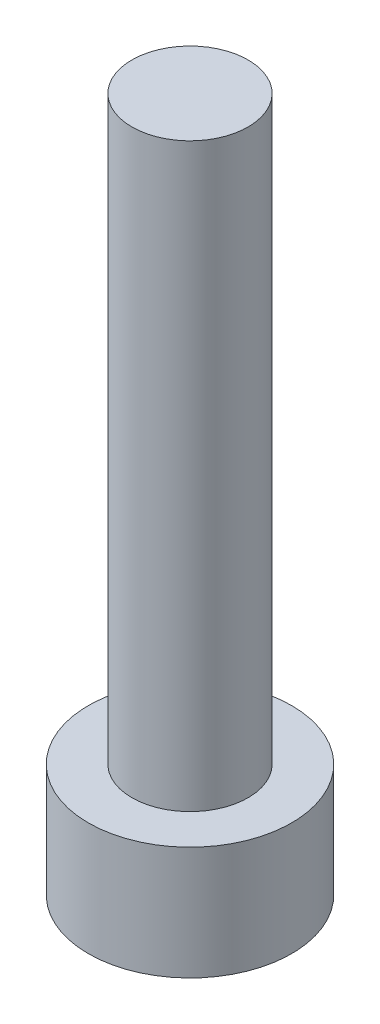
SolidWorks part; units mm, degrees
ref_plane "前视基准面" through (0, 0, 0) normal (0, 0, 1) x (1, 0, 0)
ref_plane "上视基准面" through (0, 0, 0) normal (0, 1, 0) x (1, 0, 0)
ref_plane "右视基准面" through (0, 0, 0) normal (1, 0, 0) x (0, 0, -1)
sketch "草图1" plane through (0, 0, 0) normal (0, 1, 0) x (1, 0, 0)
  circle A0 centre (0, 0) radius 3.5
extrude "凸台-拉伸1" add sketch "草图1" along normal blind 3.9
sketch "草图2" plane through (0, 3.9, 0) normal (0, 1, 0) x (1, 0, 0)
  circle A0 centre (0, 0) radius 2
extrude "凸台-拉伸2" add sketch "草图2" along normal blind 20
sketch "草图3" plane through (0, 0, 0) normal (0, -1, 0) x (1, 0, 0)
  line L1 (1.725, 0) -> (0.8625, 1.4939)
  line L2 (0.8625, 1.4939) -> (-0.8625, 1.4939)
  line L3 (-0.8625, 1.4939) -> (-1.725, 0)
  line L4 (-1.725, 0) -> (-0.8625, -1.4939)
  line L5 (-0.8625, -1.4939) -> (0.8625, -1.4939)
  line L6 (0.8625, -1.4939) -> (1.725, 0)
  circle A0 centre (0, 0) radius 1.4939 construction
extrude "切除-拉伸1" cut sketch "草图3" against normal blind 2.4
